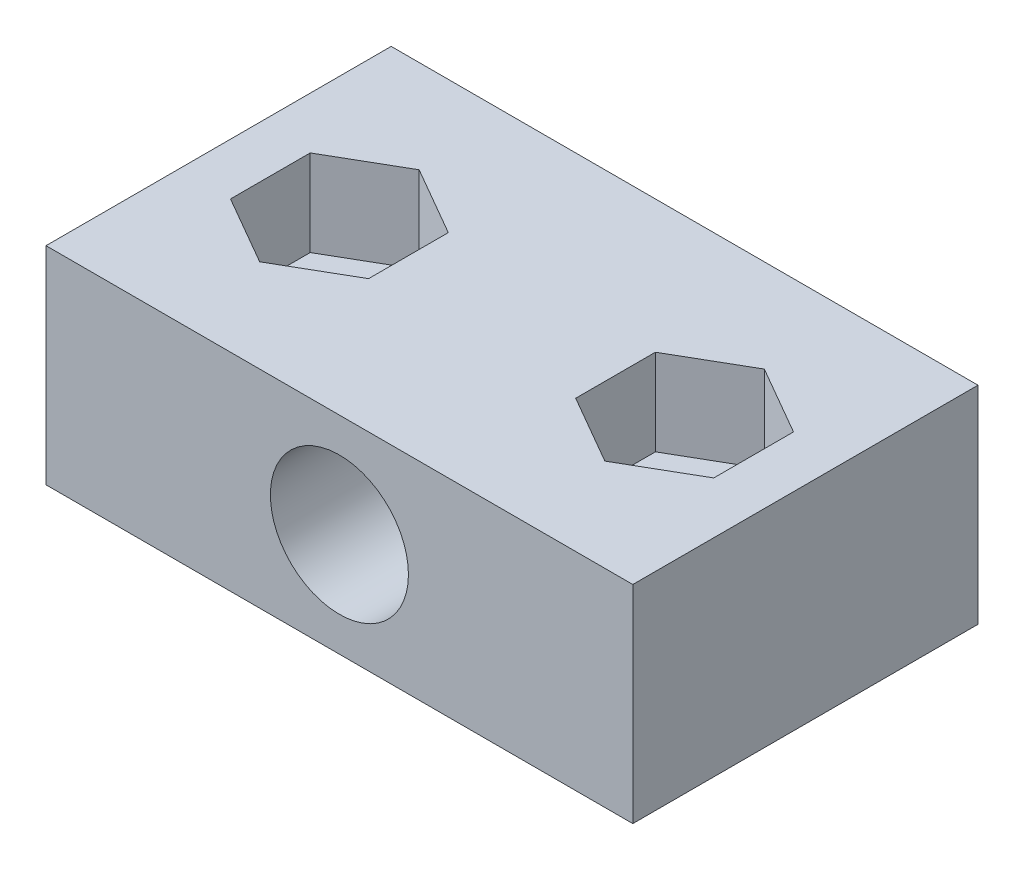
SolidWorks part; units mm, degrees
material "Delrin 2700 NC010, Low Viscosity Acetal Copolymer (SS)"
ref_plane "Front Plane" through (0, 0, 0) normal (0, 0, 1) x (1, 0, 0)
ref_plane "Top Plane" through (0, 0, 0) normal (0, 1, 0) x (1, 0, 0)
ref_plane "Right Plane" through (0, 0, 0) normal (1, 0, 0) x (0, 0, -1)
sketch "Sketch1" plane through (0, 0, 0) normal (0, 0, 1) x (1, 0, 0)
  line L1 (17, -6) -> (-17, -6)
  line L2 (17, -6) -> (17, 6)
  line L3 (17, 6) -> (-17, 6)
  line L4 (-17, -6) -> (-17, 6)
  line L5 (17, -6) -> (-17, 6) construction
  line L6 (17, 6) -> (-17, -6) construction
  point P0 (0, 0)
  dimension "D1" = 12
  dimension "D2" = 34
extrude "Boss-Extrude1" add sketch "Sketch1" along normal blind 20
sketch "Sketch2" plane through (0, 0, 20) normal (0, 0, 1) x (1, 0, 0)
  circle A0 centre (0, 0) radius 4
  dimension "D1" = 8
extrude "Cut-Extrude1" cut sketch "Sketch2" against normal through all
sketch "Sketch3" plane through (0, 6, 0) normal (0, 1, 0) x (1, 0, 0)
  line L0 (-17, -10) -> (0, -10) construction
  line L1 (0, -10) -> (0, 0) construction
  line L2 (-17, -20) -> (-17, 0) construction
  circle A0 centre (-10, -10) radius 2.55
  circle A1 centre (10, -10) radius 2.55
  dimension "D1" = 5.1
  dimension "D2" = 20
extrude "Cut-Extrude2" cut sketch "Sketch3" against normal through all
sketch "Sketch4" plane through (0, 6, 0) normal (0, 1, 0) x (1, 0, 0)
  line L0 (0, 0) -> (0, 6.2689) construction
  line L1 (-10, -5.3812) -> (-14, -7.6906)
  line L2 (-14, -7.6906) -> (-14, -12.3094)
  line L3 (-14, -12.3094) -> (-10, -14.6188)
  line L4 (-10, -14.6188) -> (-6, -12.3094)
  line L5 (-6, -12.3094) -> (-6, -7.6906)
  line L6 (-6, -7.6906) -> (-10, -5.3812)
  line L7 (6, -7.6906) -> (10, -5.3812)
  line L8 (6, -12.3094) -> (6, -7.6906)
  line L9 (10, -14.6188) -> (6, -12.3094)
  line L10 (14, -12.3094) -> (10, -14.6188)
  line L11 (14, -7.6906) -> (14, -12.3094)
  line L12 (10, -5.3812) -> (14, -7.6906)
  circle A0 centre (-10, -10) radius 4 construction
  circle A1 centre (10, -10) radius 4 construction
  dimension "D1" = 8
extrude "Cut-Extrude3" cut sketch "Sketch4" against normal blind 5
sketch "Sketch5" plane through (0, -6, 0) normal (0, -1, 0) x (1, 0, 0)
  circle A0 centre (10, 10) radius 4.5
  circle A1 centre (-10, 10) radius 4.5
  dimension "D1" = 9
extrude "Cut-Extrude4" cut sketch "Sketch5" against normal blind 2
sketch "Sketch6" plane through (0, -6, 0) normal (0, -1, 0) x (-1, 0, 0)
  line L0 (0, 0) -> (0, -28.2908) construction
  line L1 (17, 0) -> (-17, 0) construction
